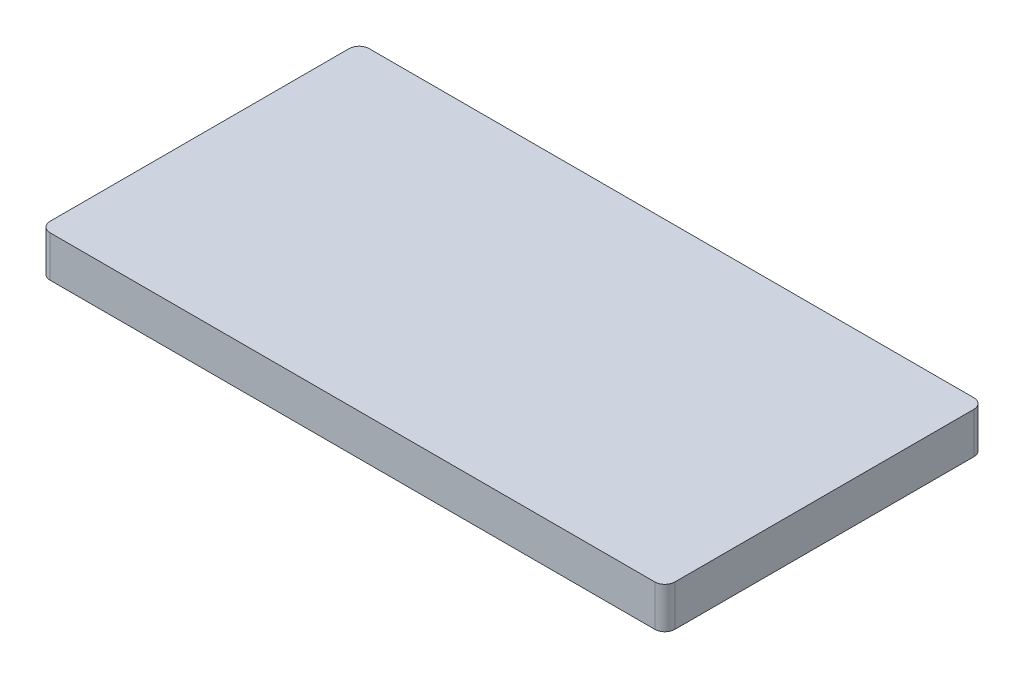
SolidWorks part; units mm, degrees
ref_plane "Front Plane" through (0, 0, 0) normal (0, 0, 1) x (1, 0, 0)
ref_plane "Top Plane" through (0, 0, 0) normal (0, 1, 0) x (1, 0, 0)
ref_plane "Right Plane" through (0, 0, 0) normal (1, 0, 0) x (0, 0, -1)
sketch "Sketch1" plane through (0, 0, 0) normal (0, 1, 0) x (1, 0, 0)
  line L1 (-57.8943, 32.9348) -> (66.7557, 32.9348)
  line L2 (-57.8943, 32.9348) -> (-57.8943, -30.7152)
  line L3 (-57.8943, -30.7152) -> (66.7557, -30.7152)
  line L4 (66.7557, 32.9348) -> (66.7557, -30.7152)
  dimension "D1" = 124.65
  dimension "D2" = 63.65
extrude "Boss-Extrude1" add sketch "Sketch1" along normal blind 8.2
sketch "Sketch2" plane through (-57.8943, 0, 0) normal (-1, 0, 0) x (0, 0, 1)
  line L0 (-32.9348, 0) -> (30.7152, 0) construction
  line L1 (-4.9698, 5.45) -> (2.7502, 5.45)
  line L2 (-4.9698, 5.45) -> (-4.9698, 2.75)
  line L3 (-4.9698, 2.75) -> (2.7502, 2.75)
  line L4 (2.7502, 5.45) -> (2.7502, 2.75)
  line L5 (30.7152, 8.2) -> (30.7152, 0) construction
  line L6 (12.07, 6.75) -> (24.37, 6.75)
  line L7 (12.07, 6.75) -> (12.07, 1.45)
  line L8 (12.07, 1.45) -> (24.37, 1.45)
  line L9 (24.37, 6.75) -> (24.37, 1.45)
  point P6 (-1.1098, 2.75)
  point P7 (-1.1098, 0)
  point P12 (2.7502, 4.1)
  point P13 (12.07, 4.1)
  point P16 (24.37, 4.1)
  point P17 (30.7152, 4.1)
  dimension "D1" = 7.72
  dimension "D2" = 2.7
  dimension "D3" = 12.3
  dimension "D4" = 5.3
extrude "Cut-Extrude1" cut sketch "Sketch2" against normal blind 12
sketch "Sketch3" plane through (0, 0, 0) normal (0, -1, 0) x (1, 0, 0)
  line L0 (-57.8943, -32.9348) -> (-57.8943, 30.7152) construction
  line L1 (-46.6943, -14.9348) -> (-45.6943, -14.9348)
  line L2 (-46.6943, -14.9348) -> (-46.6943, -23.9348)
  line L3 (-46.6943, -23.9348) -> (-45.6943, -23.9348)
  line L4 (-45.6943, -14.9348) -> (-45.6943, -23.9348)
  line L5 (66.7557, -32.9348) -> (-57.8943, -32.9348) construction
  dimension "D1" = 1
  dimension "D2" = 9
  dimension "D3" = 11.2
  dimension "D4" = 9
extrude "Cut-Extrude2" cut sketch "Sketch3" against normal blind 1
fillet "Fillet1" radius 2 4 edges at (66.7557, 4.1, 30.7152) (66.7557, 4.1, -32.9348) (-57.8943, 4.1, -32.9348) (-57.8943, 4.1, 30.7152)
